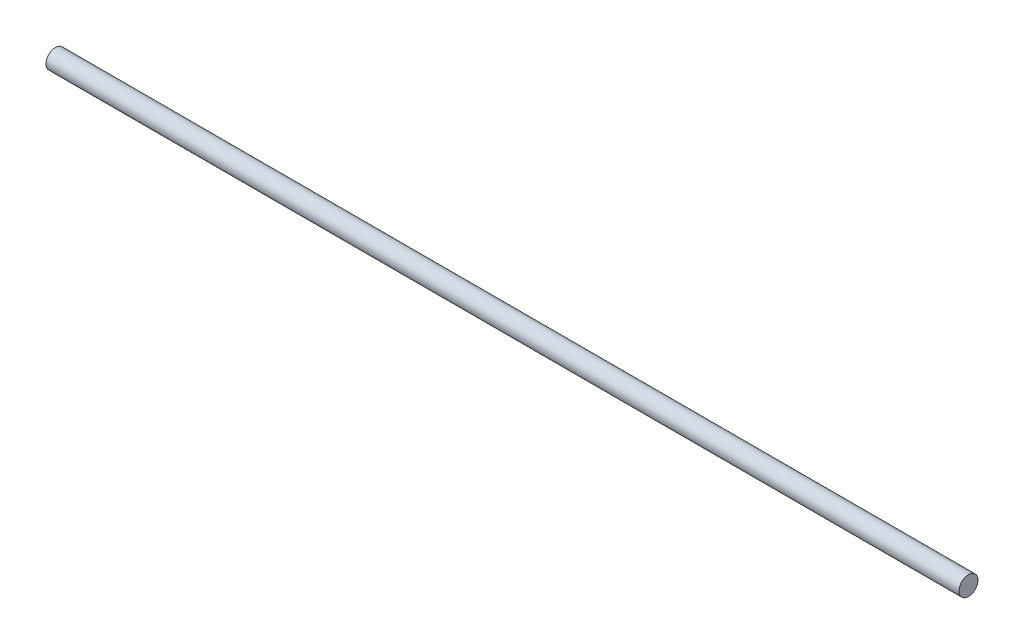
SolidWorks part; units mm, degrees
ref_plane "Front Plane" through (0, 0, 0) normal (0, 0, 1) x (1, 0, 0)
ref_plane "Top Plane" through (0, 0, 0) normal (0, 1, 0) x (1, 0, 0)
ref_plane "Right Plane" through (0, 0, 0) normal (1, 0, 0) x (0, 0, -1)
sketch "Sketch1" plane through (0, 0, 0) normal (1, 0, 0) x (0, 0, -1)
  circle A0 centre (0, 0) radius 3.175
  dimension "D1" = 6.35
extrude "Boss-Extrude1" add sketch "Sketch1" along normal blind 304.8
